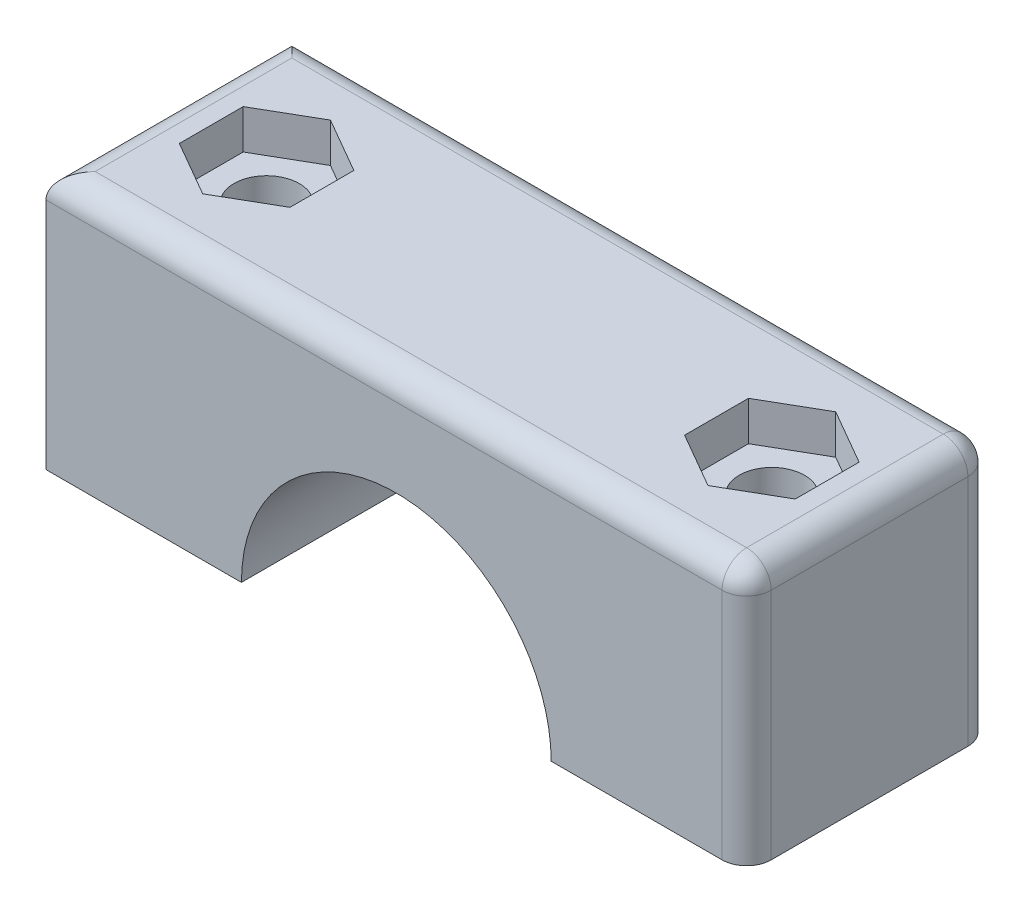
SolidWorks part; units mm, degrees
ref_plane "Front Plane" through (0, 0, 0) normal (0, 0, 1) x (1, 0, 0)
ref_plane "Top Plane" through (0, 0, 0) normal (0, 1, 0) x (1, 0, 0)
ref_plane "Right Plane" through (0, 0, 0) normal (1, 0, 0) x (0, 0, -1)
sketch "Sketch3" plane through (0, 0, 0) normal (0, 0, 1) x (1, 0, 0)
  line L1 (-36.195, 13.335) -> (36.195, 13.335)
  line L2 (-36.195, 13.335) -> (-36.195, -13.335)
  line L3 (-36.195, -13.335) -> (36.195, -13.335)
  line L4 (36.195, 13.335) -> (36.195, -13.335)
  line L5 (-36.195, 13.335) -> (36.195, -13.335) construction
  line L6 (-36.195, -13.335) -> (36.195, 13.335) construction
  point P0 (0, 0)
  dimension "D1" = 72.39
  dimension "D2" = 26.67
extrude "Boss-Extrude1" add sketch "Sketch3" along normal mid plane 25.4
sketch "Sketch4" plane through (0, 0, 12.7) normal (0, 0, 1) x (1, 0, 0)
  line L0 (-36.195, -13.335) -> (36.195, -13.335) construction
  circle A0 centre (0, -13.335) radius 16.002
  dimension "D1" = 32.004
extrude "Cut-Extrude1" cut sketch "Sketch4" against normal through all
sketch "Sketch7" plane through (0, 0, 0) normal (0, 1, 0) x (1, 0, 0)
  line L0 (-26.1019, -0.7988) -> (-26.1019, 0) construction
  line L1 (-14.6685, 0) -> (14.6685, 0) construction
  line L2 (-26.1019, 0) -> (-36.2619, 0) construction
  circle A0 centre (-26.1019, 0) radius 3.3782
  dimension "D1" = 6.7564
  dimension "D2" = 10.16
ref_plane "Plane1" through (-16.002, 0, 0) normal (1, 0, 0) x (0, 0, -1)
extrude "Cut-Extrude2" cut sketch "Sketch7" against normal mid plane 31.75
mirror "Mirror1" about plane through (0, 0, 0) normal (1, 0, 0) of "Cut-Extrude2"
fillet "Fillet1" radius 2.54 6 edges at (36.195, 0, -12.7) (36.195, 0, 12.7) (36.195, 13.335, 0) (-36.195, 13.335, 0) (0, 13.335, -12.7) (0, 13.335, 12.7)
sketch "Sketch8" plane through (0, 13.335, 0) normal (0, 1, 0) x (1, 0, 0)
  line L1 (-26.1019, -6.5991) -> (-20.3869, -3.2996)
  line L2 (-20.3869, -3.2996) -> (-20.3869, 3.2996)
  line L3 (-20.3869, 3.2996) -> (-26.1019, 6.5991)
  line L4 (-26.1019, 6.5991) -> (-31.8169, 3.2996)
  line L5 (-31.8169, 3.2996) -> (-31.8169, -3.2996)
  line L6 (-31.8169, -3.2996) -> (-26.1019, -6.5991)
  circle A0 centre (-26.1019, 0) radius 5.715 construction
  circle A1 centre (-26.1019, 0) radius 5.715 construction
  dimension "D1" = 11.43
extrude "Cut-Extrude3" cut sketch "Sketch8" against normal blind 4.064
mirror "Mirror2" about plane through (0, 0, 0) normal (1, 0, 0) of "Cut-Extrude3"
